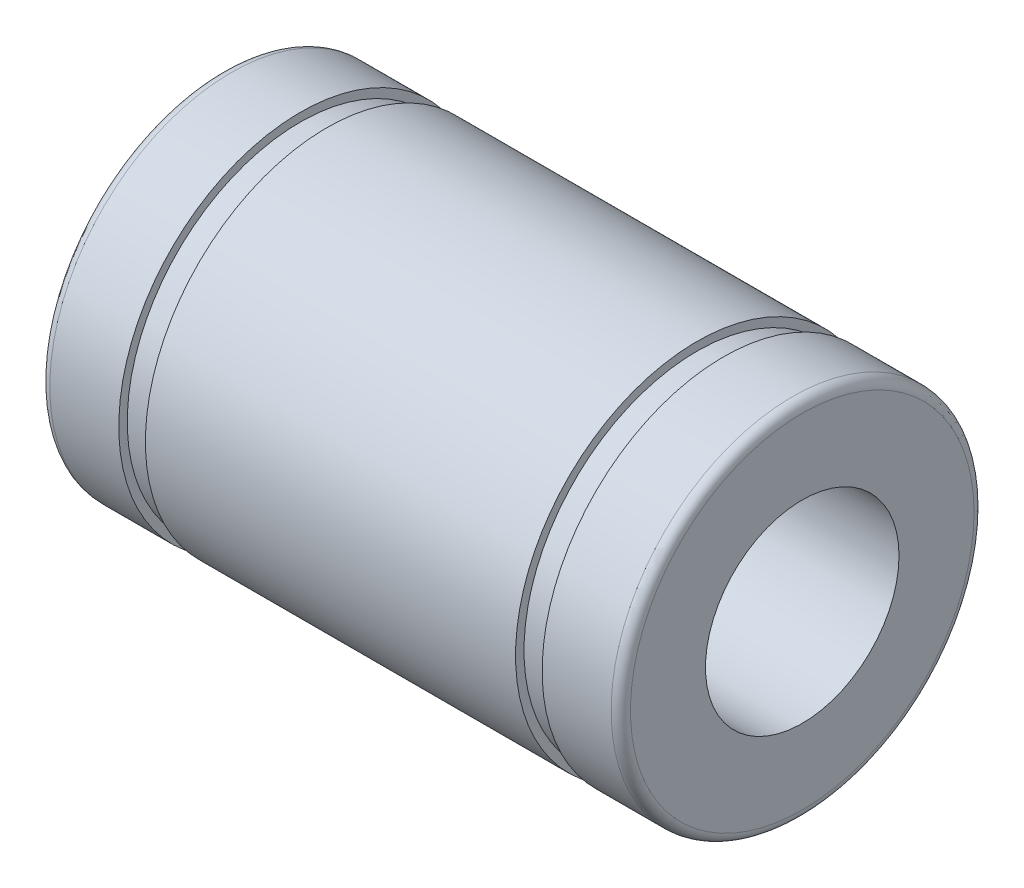
SolidWorks part; units mm, degrees
ref_plane "Front Plane" through (0, 0, 0) normal (0, 0, 1) x (1, 0, 0)
ref_plane "Top Plane" through (0, 0, 0) normal (0, 1, 0) x (1, 0, 0)
ref_plane "Right Plane" through (0, 0, 0) normal (1, 0, 0) x (0, 0, -1)
sketch "Sketch1" plane through (0, 0, 0) normal (0, 0, 1) x (1, 0, 0)
  line L0 (0, 7.1) -> (0, 4)
  line L1 (0, 4) -> (24, 4)
  line L2 (24, 4) -> (24, 7.1)
  line L3 (23.6, 7.5) -> (20.75, 7.5)
  line L4 (20.75, 7.5) -> (20.75, 7.15)
  line L5 (20.75, 7.15) -> (19.65, 7.15)
  line L6 (19.65, 7.15) -> (19.65, 7.5)
  line L7 (19.65, 7.5) -> (4.35, 7.5)
  line L8 (4.35, 7.5) -> (4.35, 7.15)
  line L9 (4.35, 7.15) -> (3.25, 7.15)
  line L10 (3.25, 7.15) -> (3.25, 7.5)
  line L11 (3.25, 7.5) -> (0.4, 7.5)
  line L12 (-0.0013, 0) -> (24.0013, 0) construction
  arc A0 (24, 7.1) -> (23.6, 7.5) centre (23.6, 7.1) ccw
  arc A1 (0.4, 7.5) -> (0, 7.1) centre (0.4, 7.1) ccw
revolve "Revolve1" add sketch "Sketch1" angle 360 about L12
